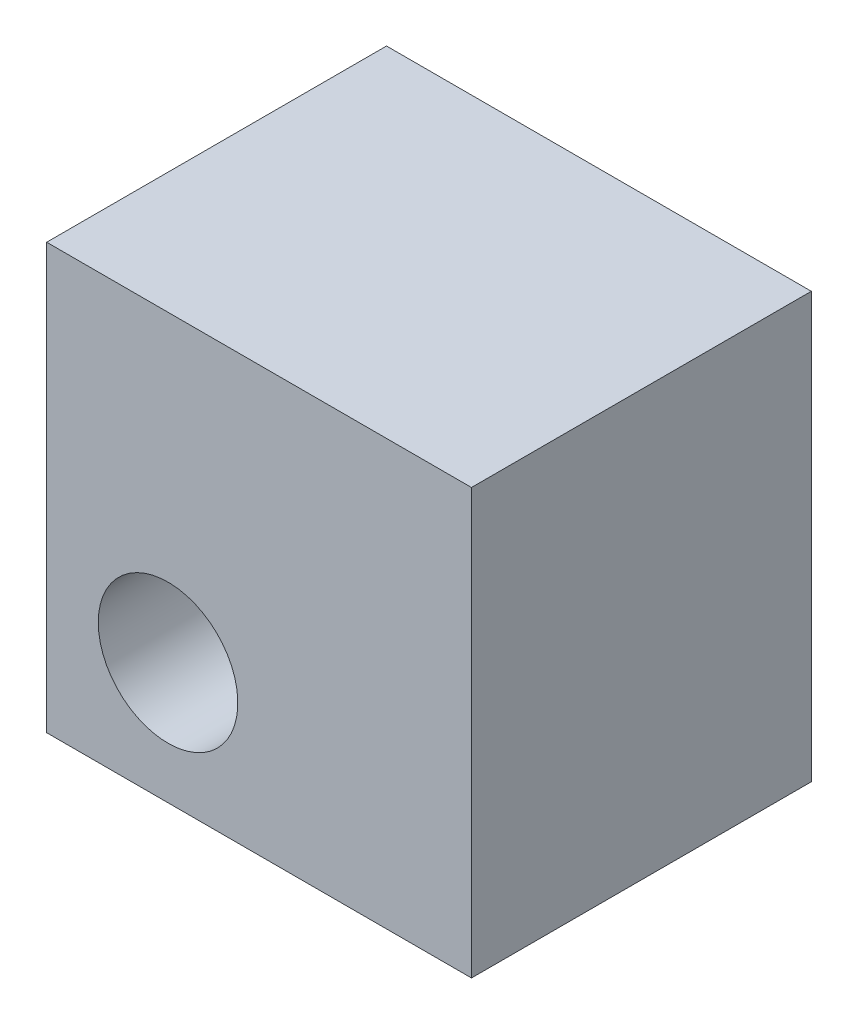
SolidWorks part; units mm, degrees
ref_plane "Front" through (0, 0, 0) normal (0, 0, 1) x (1, 0, 0)
ref_plane "Top" through (0, 0, 0) normal (0, 1, 0) x (1, 0, 0)
ref_plane "Right" through (0, 0, 0) normal (1, 0, 0) x (0, 0, -1)
sketch "Esquisse1" plane through (0, 0, 0) normal (0, 0, 1) x (1, 0, 0)
  line L1 (0, 0) -> (7, 0)
  line L2 (0, 0) -> (0, 7)
  line L3 (0, 7) -> (7, 7)
  line L4 (7, 0) -> (7, 7)
  dimension "D1" = 7
  dimension "D2" = 7
extrude "Boss.-Extru.1" add sketch "Esquisse1" along normal blind 5.6
sketch "Esquisse2" plane through (0, 0, 0) normal (0, 0, 1) x (1, 0, 0)
  line L1 (0, 0) -> (4.5, 0)
  line L2 (0, 0) -> (0, 4.5)
  line L3 (0, 4.5) -> (4.5, 4.5)
  line L4 (4.5, 0) -> (4.5, 4.5)
  dimension "D1" = 4.5
  dimension "D2" = 4.5
extrude "Enlèv. mat.-Extru.1" cut sketch "Esquisse2" along normal blind 1.6
sketch "Esquisse3" plane through (0, 0, 0) normal (0, 0, 1) x (1, 0, 0)
  line L1 (4.5, 0) -> (4.5, 4.5) construction
  line L2 (4.5, 4.5) -> (0, 4.5) construction
  circle A0 centre (2, 2) radius 1.15
  dimension "D1" = 2.3
  dimension "D2" = 2.5
  dimension "D3" = 2.5
extrude "Enlèv. mat.-Extru.2" cut sketch "Esquisse3" along normal blind 11.6
